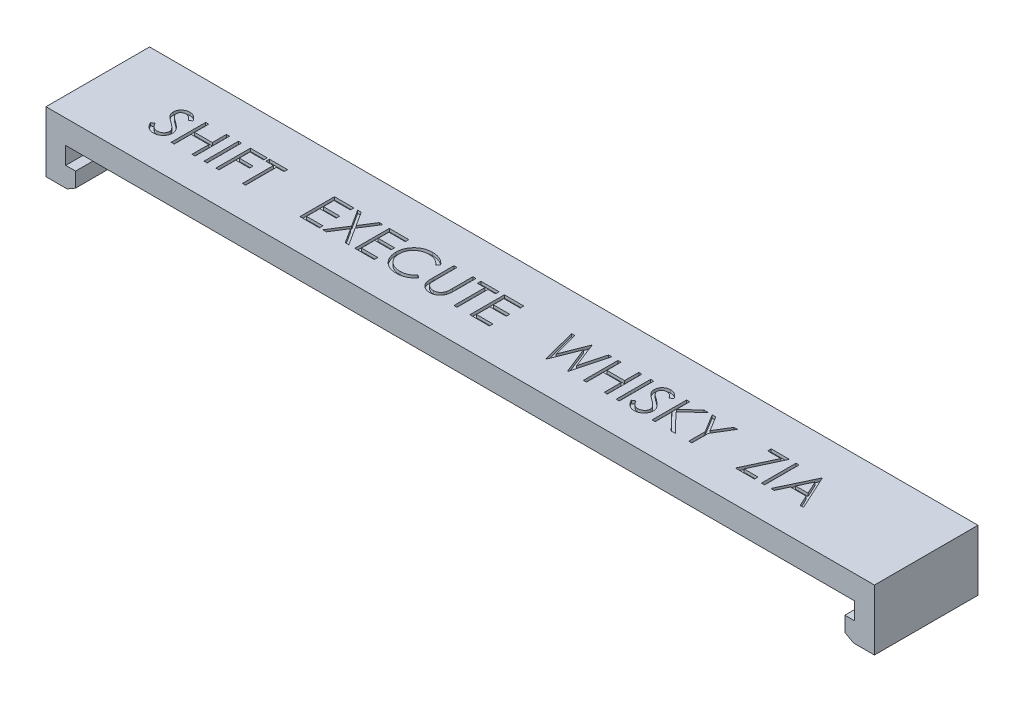
SolidWorks part; units mm, degrees
ref_plane "Front Plane" through (0, 0, 0) normal (0, 0, 1) x (1, 0, 0)
ref_plane "Top Plane" through (0, 0, 0) normal (0, 1, 0) x (1, 0, 0)
ref_plane "Right Plane" through (0, 0, 0) normal (1, 0, 0) x (0, 0, -1)
sketch "Sketch1" plane through (0, 0, 0) normal (0, 1, 0) x (1, 0, 0)
  line L1 (-40, -5.25) -> (40, -5.25)
  line L2 (-40, -5.25) -> (-40, 5.25)
  line L3 (-40, 5.25) -> (40, 5.25)
  line L4 (40, -5.25) -> (40, 5.25)
  line L5 (-40, -5.25) -> (40, 5.25) construction
  line L6 (-40, 5.25) -> (40, -5.25) construction
  point P0 (0, 0)
  dimension "D1" = 80
  dimension "D2" = 10.5
extrude "Boss-Extrude1" add sketch "Sketch1" along normal blind 2.4
sketch "Sketch2" plane through (40, 0, 0) normal (1, 0, 0) x (0, 0, -1)
  line L0 (-5.25, 2.4) -> (-5.25, 0) construction
  line L1 (5.25, 2.4) -> (-5.25, 2.4)
  line L2 (5.25, 2.4) -> (5.25, -1.75)
  line L3 (5.25, -1.75) -> (-5.25, -1.75)
  line L4 (-5.25, 2.4) -> (-5.25, -1.75)
  line L5 (-5.25, 0) -> (5.25, 0) construction
  dimension "D1" = 1.75
extrude "Boss-Extrude2" add sketch "Sketch2" along normal blind 2
sketch "Sketch3" plane through (-40, 0, 0) normal (-1, 0, 0) x (0, 0, 1)
  line L0 (5.25, 2.4) -> (5.25, 0) construction
  line L1 (-5.25, 2.4) -> (5.25, 2.4)
  line L2 (-5.25, 2.4) -> (-5.25, -1.75)
  line L3 (-5.25, -1.75) -> (5.25, -1.75)
  line L4 (5.25, 2.4) -> (5.25, -1.75)
  line L5 (-5.25, 0) -> (5.25, 0) construction
  dimension "D1" = 1.75
extrude "Boss-Extrude3" add sketch "Sketch3" along normal blind 2
sketch "Sketch4" plane through (0, -1.75, 0) normal (0, -1, 0) x (1, 0, 0)
  line L0 (42, -5.25) -> (40, -5.25) construction
  line L1 (-42, 5.25) -> (-39, 5.25)
  line L2 (-42, 5.25) -> (-42, -5.25)
  line L3 (-42, -5.25) -> (-39, -5.25)
  line L4 (-39, 5.25) -> (-39, -5.25)
  line L5 (42, 5.25) -> (39, 5.25)
  line L6 (42, 5.25) -> (42, -5.25)
  line L7 (42, -5.25) -> (39, -5.25)
  line L8 (39, 5.25) -> (39, -5.25)
  line L9 (-42, -5.25) -> (-40, -5.25) construction
  dimension "D1" = 3
  dimension "D2" = 3
extrude "Boss-Extrude4" add sketch "Sketch4" along normal blind 2
chamfer "Chamfer1" distance 0.5 angle 60 2 edges at (39, -3.75, 0) (-39, -3.75, 0)
sketch "Sketch5" plane through (0, 0, 0) normal (0, -1, 0) x (1, 0, 0)
  line L0 (-40, 5.25) -> (40, 5.25) construction
  line L1 (-40, 2.95) -> (40, 2.95)
  line L2 (-40, 2.95) -> (-40, -3.45)
  line L3 (-40, -3.45) -> (40, -3.45)
  line L4 (40, 2.95) -> (40, -3.45)
  line L5 (-40, -5.25) -> (-40, 5.25) construction
  line L6 (40, 5.25) -> (40, -5.25) construction
  dimension "D1" = 6.4
  dimension "D2" = 2.3
extrude "Cut-Extrude1" cut sketch "Sketch5" against normal blind 1.7
sketch "Sketch6" plane through (0, 2.4, 0) normal (0, 1, 0) x (1, 0, 0)
  line L0 (-46.7552, -2.0265) -> (45.1104, -2.0265) construction
  text T0 "SHIFT"
  text T1 "EXECUTE"
  text T2 "WHISKY"
  text T3 "ZIA"
extrude "Cut-Extrude2" cut sketch "Sketch6" against normal blind 0.3
